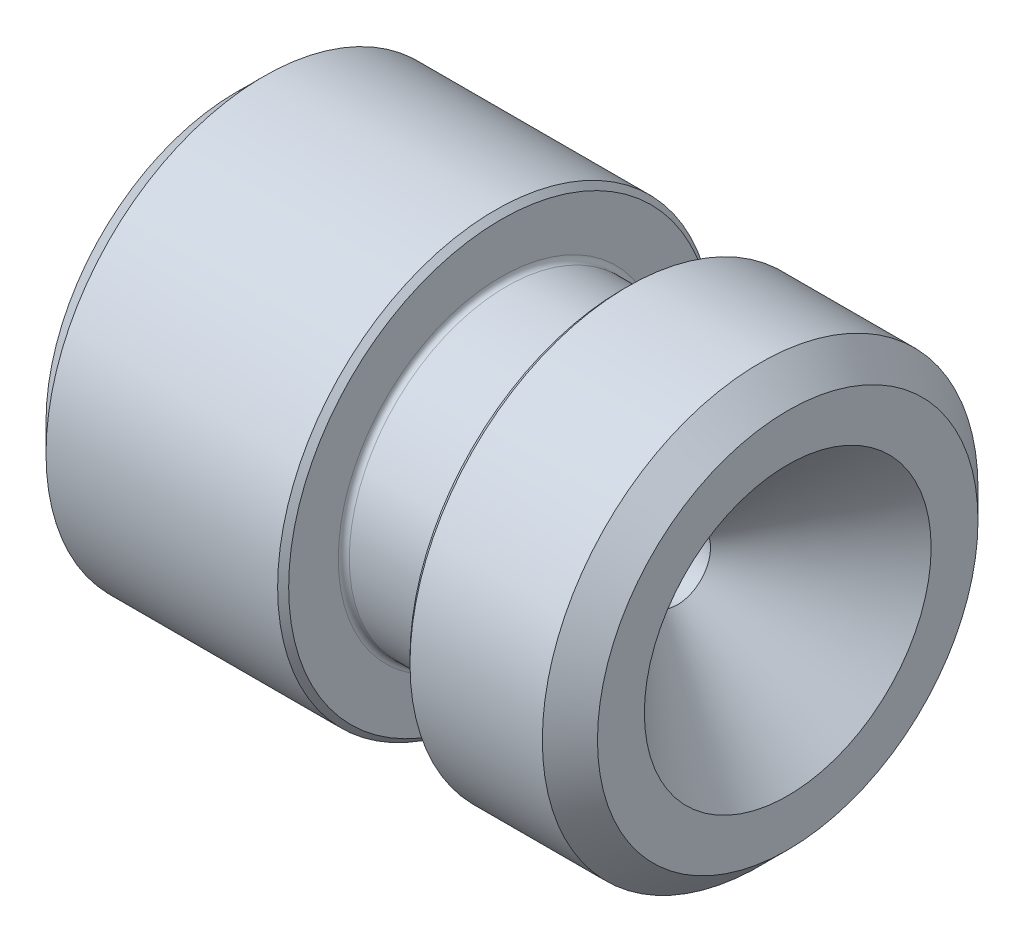
SolidWorks part; units mm, degrees
material "7075-T6 (SN)"
ref_plane "Front Plane" through (0, 0, 0) normal (0, 0, 1) x (1, 0, 0)
ref_plane "Top Plane" through (0, 0, 0) normal (0, 1, 0) x (1, 0, 0)
ref_plane "Right Plane" through (0, 0, 0) normal (1, 0, 0) x (0, 0, -1)
sketch "Sketch1" plane through (0, 0, 0) normal (0, 0, 1) x (1, 0, 0)
  line L0 (-8, -2.7436) -> (-8, -3.95)
  line L3 (2, -2.6) -> (0, -0.6)
  line L4 (0, -0.6) -> (-8, -2.7436)
  line L5 (-24.2985, 0) -> (27.1588, 0) construction
  line L6 (2, -2.6) -> (2, -3.95)
  line L7 (2, -3.95) -> (-1, -3.95)
  line L9 (-8, -3.95) -> (-3.2, -3.95)
  line L10 (-3.2, -3.95) -> (-3.2, -2.85)
  line L11 (-3.2, -2.85) -> (-1, -2.85)
  line L12 (-1, -2.85) -> (-1, -3.95)
  dimension "D1" = 1.2
  dimension "D2" = 5.7
  dimension "D3" = 10
  dimension "D4" = 45
  dimension "D5" = 7.9
  dimension "D6" = 3
  dimension "D7" = 2.2
  dimension "D11" = 8
  dimension "D12" = 15
  dimension "D13" = 5.2
  dimension "D14" = 5.4872
revolve "Revolve1" add sketch "Sketch1" angle 360 about L5
chamfer "Chamfer1" distance 0.5 angle 45 2 edges at (-8, 0, 3.95) (2, 0, 3.95)
fillet "Fillet1" radius 0.1 2 edges at (-3.2, 0, 2.85) (-1, 0, 2.85)
chamfer "Chamfer2" distance 0.1 angle 45 2 edges at (-1, 0, 3.95) (-3.2, 0, 3.95)
